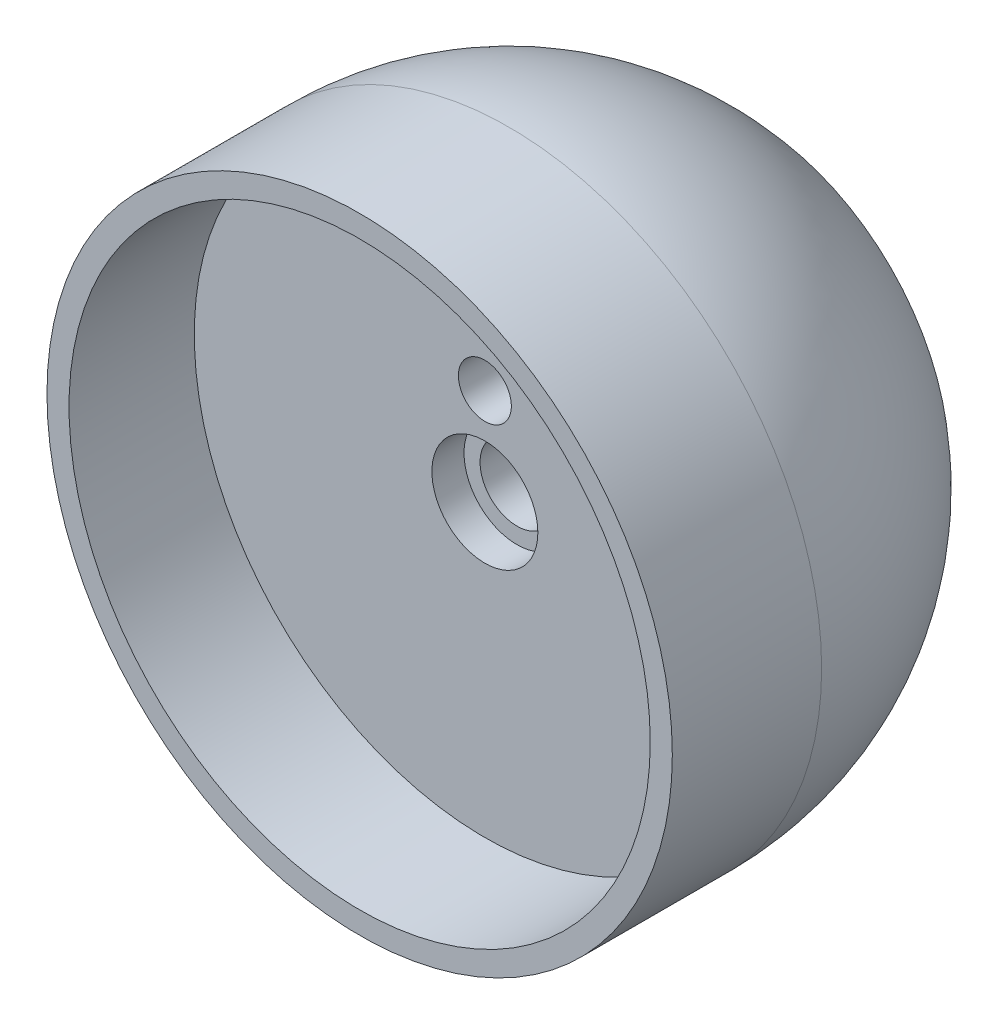
SolidWorks part; units mm, degrees
ref_plane "Front Plane" through (0, 0, 0) normal (0, 0, 1) x (1, 0, 0)
ref_plane "Top Plane" through (0, 0, 0) normal (0, 1, 0) x (1, 0, 0)
ref_plane "Right Plane" through (0, 0, 0) normal (1, 0, 0) x (0, 0, -1)
sketch "Sketch1" plane through (0, 0, 0) normal (0, 0, 1) x (1, 0, 0)
  circle A0 centre (0, 0) radius 49.4665
  dimension "D1" = 98.933
extrude "Boss-Extrude1" add sketch "Sketch1" along normal blind 23.622
sketch "Sketch2" plane through (0, 0, 23.622) normal (0, 0, 1) x (1, 0, 0)
  circle A1 centre (0, 0) radius 45.974
  dimension "D1" = 91.948
extrude "Cut-Extrude2" cut sketch "Sketch2" against normal blind 19.812
sketch "Sketch3" plane through (0, 0, 0) normal (0, 1, 0) x (1, 0, 0)
  line L0 (0, 0) -> (-49.4665, 0)
  line L1 (0, 0) -> (0, 49.4665)
  arc A0 (0, 49.4665) -> (-49.4665, 0) centre (0, 0) ccw
revolve "Revolve1" add sketch "Sketch3" angle 360 about L1
sketch "Sketch4" plane through (0, 0, 0) normal (0, 1, 0) x (1, 0, 0)
  line L1 (44.6512, 114.3) -> (-31.5488, 114.3)
  line L2 (44.6512, 114.3) -> (44.6512, 38.1)
  line L3 (44.6512, 38.1) -> (-31.5488, 38.1)
  line L4 (-31.5488, 114.3) -> (-31.5488, 38.1)
  arc A0 (49.4665, 0) -> (-49.4665, 0) centre (0, 0) ccw construction
  dimension "D1" = 76.2
  dimension "D2" = 76.2
  dimension "D3" = 38.1
extrude "Cut-Extrude3" cut sketch "Sketch4" against normal through all and the other way through all
sketch "Sketch5" plane through (0, 0, 3.81) normal (0, 0, 1) x (1, 0, 0)
  circle A0 centre (0, 0) radius 8.382
  dimension "D1" = 16.764
extrude "Cut-Extrude4" cut sketch "Sketch5" against normal blind 5.08
sketch "Sketch6" plane through (0, 0, -1.27) normal (0, 0, 1) x (1, 0, 0)
  circle A0 centre (0, 0) radius 5.842
  circle A1 centre (0, 0) radius 8.382 construction
  dimension "D1" = 2.54
extrude "Cut-Extrude5" cut sketch "Sketch6" against normal through all
sketch "Sketch7" plane through (0, 0, 3.81) normal (0, 0, 1) x (1, 0, 0)
  circle A0 centre (0, 15.24) radius 4.191
  dimension "D1" = 8.382
  dimension "D2" = 15.24
extrude "Cut-Extrude6" cut sketch "Sketch7" against normal through all
ref_plane "Jeremy" through (0, 0, -17.145) normal (0, 0, 1) x (1, 0, 0)
mirror "Mirror1" about plane through (0, 0, -17.145) normal (0, 0, 1) of "Cut-Extrude4"
